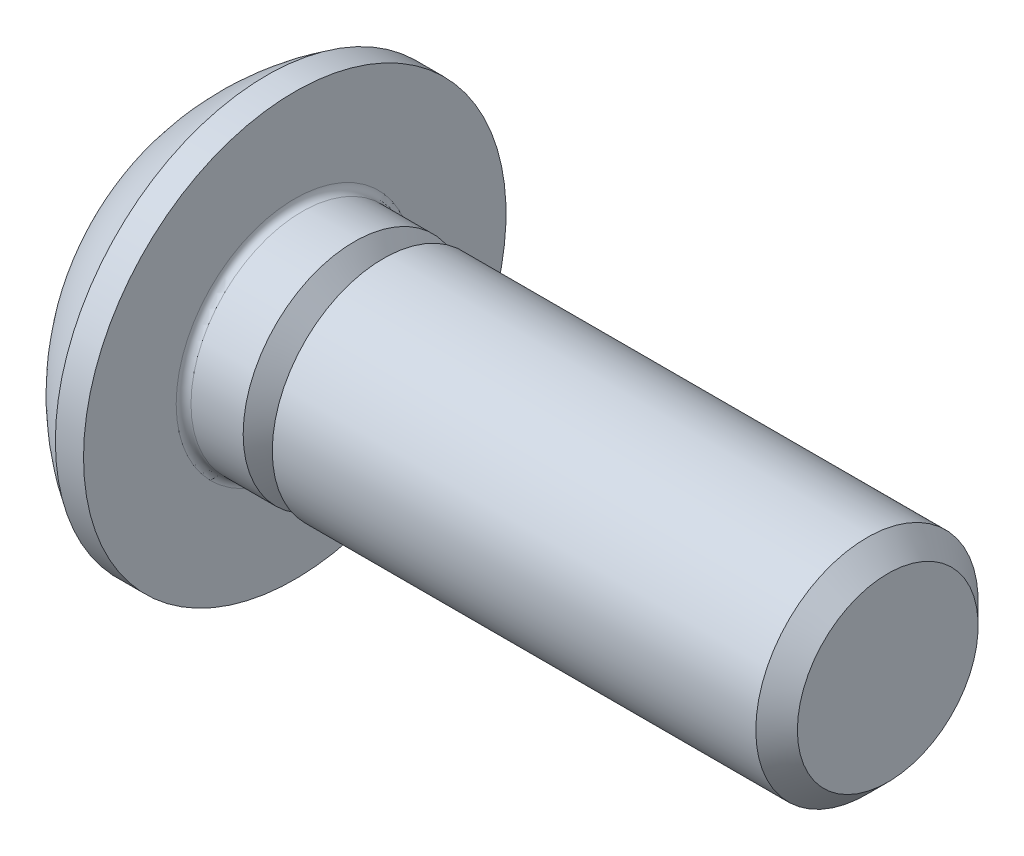
SolidWorks part; units mm, degrees
material "AISI 1045 Aço, trefilado"
ref_plane "Plane1" through (0, 0, 0) normal (0, 0, 1) x (1, 0, 0)
ref_plane "Plane2" through (0, 0, 0) normal (0, 1, 0) x (1, 0, 0)
ref_plane "Plane3" through (0, 0, 0) normal (1, 0, 0) x (0, 0, -1)
sketch "BodySke" plane through (0, 0, 0) normal (0, 0, 1) x (1, 0, 0)
  line L0 (9.65, 0) -> (9.65, 1.2195)
  line L1 (9.3695, 1.5) -> (1.65, 1.5)
  line L2 (1.65, 1.5) -> (1.65, 2.85)
  line L3 (1.65, 2.85) -> (1.27, 2.85)
  line L4 (0, 0) -> (101.6, 0) construction
  line L5 (1.65, -2.85) -> (1.27, -2.85) construction
  line L6 (55.6768, -1.5) -> (1.65, -1.5) construction
  line L7 (9.65, 0) -> (0, 0)
  line L8 (0, 1.425) -> (0, -1.425) construction
  line L9 (0, 0) -> (0, 1.425)
  line L10 (9.65, 1.2195) -> (9.3695, 1.5)
  line L11 (9.65, -1.2195) -> (9.3695, -1.5) construction
  line L12 (2.15, 9.525) -> (2.15, -1.5) construction
  line L13 (1.65, 9.525) -> (1.65, -1.5) construction
  arc A1 (0, 1.425) -> (1.27, 2.85) centre (3.0334, 0) cw
  dimension "D1" = 2.85
  dimension "Diameter" = 3
  dimension "Length" = 8
  dimension "Head_dia" = 5.7
  dimension "Head_ht" = 1.65
  dimension "Head_side_ht" = 0.38
  dimension "Minor_dia" = 2.439
  dimension "Body_ch_ang" = 45
  dimension "Advance" = 0.5
  dimension "Thread_nom" = 8
revolve "BaseBody" add sketch "BodySke" angle 360 about L4
cosmetic thread "ThreadCosmetic" [suppressed] parameters "Thread_length"=7, "Thread_minor"=2.439
fillet "Fillet1" radius 0.1 1 edges at (1.65, 0, 1.5)
sketch "Sketch2" plane through (0, 0, 0) normal (0, 0, 1) x (1, 0, 0)
  line L0 (0, 1) -> (1.04, 1)
  line L1 (1.04, 1) -> (1.6174, 0)
  line L3 (1.6174, 0) -> (0, 0)
  line L4 (0, 0) -> (0, 1)
  line L5 (0, -1) -> (1.04, -1) construction
  line L6 (0, 0) -> (47.625, 0) construction
  dimension "D2" = 60
  dimension "PreBroach_depth" = 1.04
  dimension "PreBroach_dia" = 2
revolve "PreBroach" cut sketch "Sketch2" angle 360 about L6
sketch "Sketch3" plane through (0, 0, 0) normal (1, 0, 0) x (0, 0, -1)
  line L0 (-1, -0.5774) -> (-1, 0.5774)
  line L1 (-1, 0.5774) -> (0, 1.1547)
  line L2 (0, 1.1547) -> (1, 0.5774)
  line L3 (1, 0.5774) -> (1, -0.5774)
  line L4 (1, -0.5774) -> (0, -1.1547)
  line L5 (0, -1.1547) -> (-1, -0.5774)
  dimension "D1" = 1
  dimension "D2" = 1
  dimension "D3" = 2
  dimension "Hex_size" = 2
extrude "Hex" cut sketch "Sketch3" along normal blind 1.04
sketch "ThdSchSke" plane through (0, 0, 0) normal (0, 0, 1) x (1, 0, 0)
  line L0 (2.65, -1.2195) -> (2.4536, -1.5)
  line L1 (2.65, -1.2195) -> (2.8464, -1.5)
  line L2 (2.8464, -1.5) -> (2.8464, -1.875)
  line L3 (-3.175, 0) -> (5.1513, 0) construction
  line L5 (2.8464, -1.875) -> (2.4536, -1.875)
  line L6 (2.4536, -1.875) -> (2.4536, -1.5)
  dimension "Thread_minor" = 2.439
  dimension "Diameter" = 3
  dimension "Start" = 2.65
  dimension "SideAngle" = 55
  dimension "VeeAngle" = 70
  dimension "Overcut" = 3.75
revolve "ThreadSchematic" cut sketch "ThdSchSke" angle 360 about L3
pattern_linear "ThdSchPat" [suppressed]
equation "\"D1@BodySke\" = \"Head_dia@BodySke\" * .5"
equation "\"Thread_minor@ThreadCosmetic\" = \"Minor_dia@BodySke\""
equation "\"D1@Sketch3\" = \"Hex_size@Sketch3\" / 2"
equation "\"D2@Sketch3\" = \"D1@Sketch3\""
equation "\"D3@Sketch3\" = \"Hex_size@Sketch3\""
equation "\"Thread_length@ThreadCosmetic\" = ((sgn( (\"Length@BodySke\" - \"Advance@BodySke\" * 2.0) - \"Thread_nom@BodySke\" )-1)*( (\"Length@BodySke\" - \"Advance@BodySke\" * 2.0) - \"Thread_nom@BodySke\" ))/-2+ \"Thread_nom@BodySke\""
equation "\"Thread_minor@ThdSchSke\" = \"Minor_dia@BodySke\""
equation "\"Diameter@ThdSchSke\" = \"Diameter@BodySke\""
equation "\"Overcut@ThdSchSke\" = \"Diameter@BodySke\" * 1.25"
equation "\"Start@ThdSchSke\" = \"Head_ht@BodySke\" + \"Length@BodySke\" - \"Thread_length@ThreadCosmetic\"  '---Non-countersunk---"
equation "\"Num_threads@ThdSchPat\" = int( \"Thread_length@ThreadCosmetic\" / \"Advance@BodySke\" + 0.999 )  + 1"
equation "\"Advance@ThdSchPat\" = \"Thread_length@ThreadCosmetic\" /  (\"Num_threads@ThdSchPat\" - 1) 'relax it"
equation "\"Num_threads@ThdSchPat\" = \"Num_threads@ThdSchPat\" - sgn( \"Num_threads@ThdSchPat\" - 1) '---chamfered tips only---"
